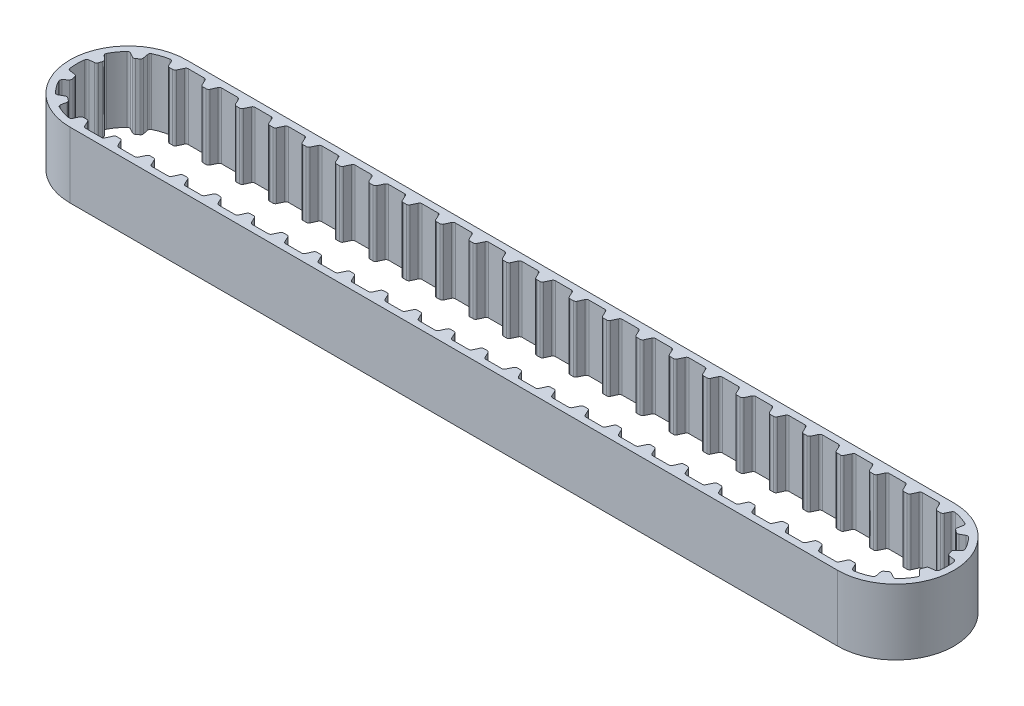
SolidWorks part; units mm, degrees
ref_plane "Front Plane" through (0, 0, 0) normal (0, 0, 1) x (1, 0, 0)
ref_plane "Top Plane" through (0, 0, 0) normal (0, 1, 0) x (1, 0, 0)
ref_plane "Right Plane" through (0, 0, 0) normal (1, 0, 0) x (0, 0, -1)
sketch "Sketch1" plane through (0, 0, 0) normal (0, 1, 0) x (1, 0, 0)
  line L0 (0, 0) -> (0, 23.0926) construction
  line L1 (0, 0) -> (116.84, 0) construction
  line L2 (0, 0) -> (0, -16.0433) construction
  line L3 (116.84, 0) -> (116.84, 15.7553) construction
  line L4 (116.84, 0) -> (116.84, -16.0433) construction
  line L5 (0, 8.86) -> (116.84, 8.86)
  line L6 (0, 7.83) -> (116.84, 7.83)
  line L7 (0, -7.83) -> (116.84, -7.83)
  line L8 (0, -8.86) -> (116.84, -8.86)
  arc A0 (0, 7.83) -> (0, -7.83) centre (0, 0) ccw
  arc A1 (0, 8.86) -> (0, -8.86) centre (0, 0) ccw
  arc A2 (116.84, -7.83) -> (116.84, 7.83) centre (116.84, 0) ccw
  arc A3 (116.84, -8.86) -> (116.84, 8.86) centre (116.84, 0) ccw
  dimension "D1" = 15.66
  dimension "D2" = 1.03
  dimension "D3" = 15.66
  dimension "D4" = 1.03
  dimension "D5" = 116.84
extrude "Boss-Extrude1" add sketch "Sketch1" along normal blind 10
sketch "Sketch2" plane through (0, 10, 0) normal (0, 1, 0) x (1, 0, 0)
  line L0 (0, 0) -> (0, 9.3992) construction
  line L1 (-0.0062, 6.56) -> (1.2728, 6.56) construction
  line L3 (-1.1688, 8) -> (-0.4888, 6.5418)
  line L4 (1.1559, 8) -> (0.4764, 6.5427)
  line L7 (-1.1688, 8) -> (1.1559, 8)
  arc A0 (-0.4888, 6.5418) -> (0.4764, 6.5427) centre (0, 0) cw
  dimension "D1" = 6.56
  dimension "D3" = 25
  dimension "D4" = 25
extrude "Boss-Extrude2" add sketch "Sketch2" against normal blind 10
pattern_circular "CirPattern1" count 6 every 36 about axis through (0, 0, 0) along (0, 1, 0) of "Boss-Extrude2"
pattern_linear "LPattern3" count 23 spacing 5.08 along (1, 0, 0) of "Boss-Extrude2"
ref_plane "Plane2" through (58.42, 0, 0) normal (1, 0, 0) x (0, 0, -1)
sketch "Sketch5" plane through (58.42, 0, 0) normal (1, 0, 0) x (0, 0, -1)
  line L0 (0, 0) -> (0.1336, 11.0556) construction
mirror "Mirror1" about plane through (58.42, 0, 0) normal (1, 0, 0) of "CirPattern1", "Boss-Extrude2"
mirror "Mirror2" about plane through (0, 0, 0) normal (0, 0, 1) of "LPattern3", "Boss-Extrude2"
fillet "Fillet1" radius 0.38 224 edges at (97.5967, 5, -7.83) (96.9964, 5, -6.5427) (96.0312, 5, -6.5418) (95.4305, 5, -7.83) (1.0895, 5, 7.83) (0.4888, 5, 6.5418) (-1.0561, 5, 7.7584) (-0.4888, 5, 6.5418) (-3.7059, 5, 6.8975) (-3.4497, 5, 5.5797) (-4.2311, 5, 5.0131) (-5.4059, 5, 5.6643) (-7.0524, 5, 3.4019) (-6.0706, 5, 2.4864) (-6.3697, 5, 1.5687) (-7.7029, 5, 1.405) (-7.7051, 5, -1.3931) (-6.3726, 5, -1.5567) (-6.0752, 5, -2.4749) (-7.0576, 5, -3.391) (-5.4147, 5, -5.6559) (-4.2406, 5, -5.0051) (-3.4603, 5, -5.5732) (-3.7166, 5, -6.8917) (-1.0561, 5, -7.7584) (-0.4888, 5, -6.5418) (0.4764, 5, -6.5427) (1.0767, 5, -7.83) (3.9905, 5, -7.83) (4.5912, 5, -6.5418) (5.5564, 5, -6.5427) (6.1567, 5, -7.83) (9.0705, 5, -7.83) (9.6712, 5, -6.5418) (10.6364, 5, -6.5427) (11.2367, 5, -7.83) (14.1505, 5, -7.83) (14.7512, 5, -6.5418) (15.7164, 5, -6.5427) (16.3167, 5, -7.83) (19.2305, 5, -7.83) (19.8312, 5, -6.5418) (20.7964, 5, -6.5427) (21.3967, 5, -7.83) (24.3105, 5, -7.83) (24.9112, 5, -6.5418) (25.8764, 5, -6.5427) (26.4767, 5, -7.83) (29.3905, 5, -7.83) (29.9912, 5, -6.5418) (30.9564, 5, -6.5427) (31.5567, 5, -7.83) (34.4705, 5, -7.83) (35.0712, 5, -6.5418) (36.0364, 5, -6.5427) (36.6367, 5, -7.83) (39.5505, 5, -7.83) (40.1512, 5, -6.5418) (41.1164, 5, -6.5427) (41.7167, 5, -7.83) (44.6305, 5, -7.83) (45.2312, 5, -6.5418) (46.1964, 5, -6.5427) (46.7967, 5, -7.83) (49.7105, 5, -7.83) (50.3112, 5, -6.5418) (51.2764, 5, -6.5427) (51.8767, 5, -7.83) (54.7905, 5, -7.83) (55.3912, 5, -6.5418) (56.3564, 5, -6.5427) (56.9567, 5, -7.83) (59.8705, 5, -7.83) (60.4712, 5, -6.5418) (61.4364, 5, -6.5427) (62.0367, 5, -7.83) (64.9505, 5, -7.83) (65.5512, 5, -6.5418) (66.5164, 5, -6.5427) (67.1167, 5, -7.83) (70.0305, 5, -7.83) (70.6312, 5, -6.5418) (71.5964, 5, -6.5427) (72.1967, 5, -7.83) (75.1105, 5, -7.83) (75.7112, 5, -6.5418) (76.6764, 5, -6.5427) (77.2767, 5, -7.83) (80.1905, 5, -7.83) (80.7912, 5, -6.5418) (81.7564, 5, -6.5427) (82.3567, 5, -7.83) (85.2705, 5, -7.83) (85.8712, 5, -6.5418) (86.8364, 5, -6.5427) (87.4367, 5, -7.83) (90.3505, 5, -7.83) (90.9512, 5, -6.5418) (91.9164, 5, -6.5427) (92.5167, 5, -7.83) (100.5105, 5, -7.83) (101.1112, 5, -6.5418) (102.0764, 5, -6.5427) (102.6767, 5, -7.83) (105.5905, 5, -7.83) (106.1912, 5, -6.5418) (107.1564, 5, -6.5427) (107.7567, 5, -7.83) (110.6705, 5, -7.83) (111.2712, 5, -6.5418) (112.2364, 5, -6.5427) (112.8367, 5, -7.83) (115.7633, 5, -7.83) (116.3636, 5, -6.5427) (117.3288, 5, -6.5418) (117.8961, 5, -7.7584) (120.5566, 5, -6.8917) (120.3003, 5, -5.5732) (121.0806, 5, -5.0051) (122.2547, 5, -5.6559) (123.8976, 5, -3.391) (122.9152, 5, -2.4749) (123.2126, 5, -1.5567) (124.5451, 5, -1.3931) (124.5429, 5, 1.405) (123.2097, 5, 1.5687) (122.9106, 5, 2.4864) (123.8924, 5, 3.4019) (122.2459, 5, 5.6643) (121.0711, 5, 5.0131) (120.2897, 5, 5.5797) (120.5459, 5, 6.8975) (117.8841, 5, 7.7601) (117.3164, 5, 6.5427) (116.3512, 5, 6.5418) (115.7505, 5, 7.83) (112.8367, 5, 7.83) (112.2364, 5, 6.5427) (111.2712, 5, 6.5418) (110.6705, 5, 7.83) (107.7567, 5, 7.83) (107.1564, 5, 6.5427) (106.1912, 5, 6.5418) (105.5905, 5, 7.83) (102.6767, 5, 7.83) (102.0764, 5, 6.5427) (101.1112, 5, 6.5418) (100.5105, 5, 7.83) (97.5967, 5, 7.83) (96.9964, 5, 6.5427) (96.0312, 5, 6.5418) (95.4305, 5, 7.83) (92.5167, 5, 7.83) (91.9164, 5, 6.5427) (90.9512, 5, 6.5418) (90.3505, 5, 7.83) (87.4367, 5, 7.83) (86.8364, 5, 6.5427) (85.8712, 5, 6.5418) (85.2705, 5, 7.83) (82.3567, 5, 7.83) (81.7564, 5, 6.5427) (80.7912, 5, 6.5418) (80.1905, 5, 7.83) (77.2767, 5, 7.83) (76.6764, 5, 6.5427) (75.7112, 5, 6.5418) (75.1105, 5, 7.83) (72.1967, 5, 7.83) (71.5964, 5, 6.5427) (70.6312, 5, 6.5418) (70.0305, 5, 7.83) (67.1167, 5, 7.83) (66.5164, 5, 6.5427) (65.5512, 5, 6.5418) (64.9505, 5, 7.83) (62.0367, 5, 7.83) (61.4364, 5, 6.5427) (60.4712, 5, 6.5418) (59.8705, 5, 7.83) (56.9567, 5, 7.83) (56.3564, 5, 6.5427) (55.3912, 5, 6.5418) (54.7905, 5, 7.83) (51.8767, 5, 7.83) (51.2764, 5, 6.5427) (50.3112, 5, 6.5418) (49.7105, 5, 7.83) (46.7967, 5, 7.83) (46.1964, 5, 6.5427) (45.2312, 5, 6.5418) (44.6305, 5, 7.83) (41.7167, 5, 7.83) (41.1164, 5, 6.5427) (40.1512, 5, 6.5418) (39.5505, 5, 7.83) (36.6367, 5, 7.83) (36.0364, 5, 6.5427) (35.0712, 5, 6.5418) (34.4705, 5, 7.83) (31.5567, 5, 7.83) (30.9564, 5, 6.5427) (29.9912, 5, 6.5418) (29.3905, 5, 7.83) (26.4767, 5, 7.83) (25.8764, 5, 6.5427) (24.9112, 5, 6.5418) (24.3105, 5, 7.83) (21.3967, 5, 7.83) (20.7964, 5, 6.5427) (19.8312, 5, 6.5418) (19.2305, 5, 7.83) (16.3167, 5, 7.83) (15.7164, 5, 6.5427) (14.7512, 5, 6.5418) (14.1505, 5, 7.83) (11.2367, 5, 7.83) (10.6364, 5, 6.5427) (9.6712, 5, 6.5418) (9.0705, 5, 7.83) (4.5912, 5, 6.5418) (3.9905, 5, 7.83) (6.1567, 5, 7.83) (5.5564, 5, 6.5427)
sketch "Sketch11" plane through (0, 10, 0) normal (0, 1, 0) x (1, 0, 0)
  line L0 (0, 0) -> (0, 21.6238) construction
  line L1 (0, 0) -> (0, -18.4344) construction
  line L2 (116.84, 0) -> (116.84, 22.9729) construction
  line L3 (116.84, 0) -> (116.84, -19.6797) construction
sketch "Sketch12" plane through (0, 10, 0) normal (0, 1, 0) x (1, 0, 0)
  line L0 (0, 0) -> (0, 20.048)
  line L1 (116.84, 0) -> (116.84, 21.7278)
